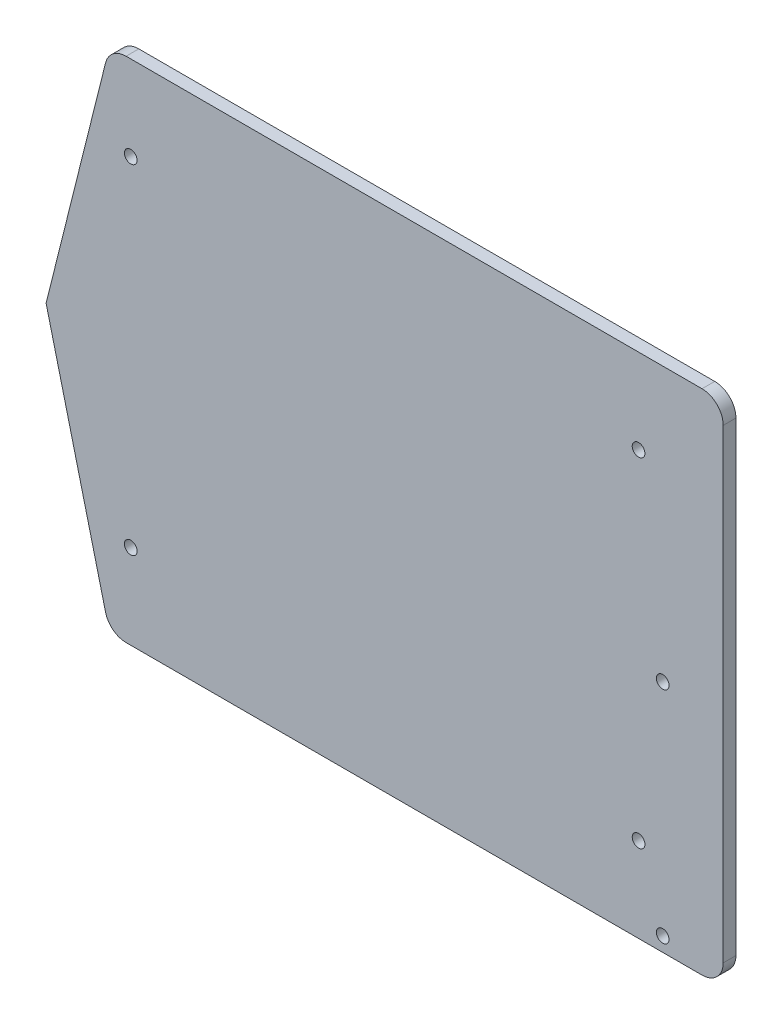
SolidWorks part; units mm, degrees
ref_plane "前基準面" through (0, 0, 0) normal (0, 0, 1) x (1, 0, 0)
ref_plane "上基準面" through (0, 0, 0) normal (0, 1, 0) x (1, 0, 0)
ref_plane "右基準面" through (0, 0, 0) normal (1, 0, 0) x (0, 0, -1)
sketch "草圖1" plane through (0, 0, 0) normal (0, 0, 1) x (1, 0, 0)
  line L1 (15, 120) -> (160, 120)
  line L2 (160, 120) -> (160, 0)
  line L3 (160, 0) -> (15, 0)
  line L4 (0, 60) -> (15, 0)
  line L6 (0, 60) -> (15, 120)
  circle A0 centre (20, 20) radius 1.5
  circle A1 centre (20, 100) radius 1.5
  circle A2 centre (140, 20) radius 1.5
  circle A3 centre (140, 100) radius 1.5
  point P7 (15, 0)
  point P9 (20, 20)
  dimension "D5" = 3
  dimension "D1" = 120
  dimension "D2" = 160
  dimension "D3" = 20
  dimension "D4" = 20
  dimension "D6" = 20
  dimension "D8" = 20
extrude "填料-伸長1" add sketch "草圖1" along normal blind 3
fillet "圓角1" radius 5 4 edges at (15, 0, 1.5) (160, 0, 1.5) (160, 120, 1.5) (15, 120, 1.5)
sketch "草圖2" plane through (0, 0, 3) normal (0, 0, 1) x (1, 0, 0)
  line L0 (160, 5) -> (160, 115) construction
  line L1 (18.9039, 0) -> (155, 0) construction
  circle A0 centre (145.7, 3.38) radius 1.5
  circle A1 centre (145.7, 55.38) radius 1.5
  point P0 (145.7, 3.38)
  point P1 (145.7, 55.38)
  dimension "D1" = 14.3
  dimension "D2" = 3.38
  dimension "D3" = 52
extrude "除料-伸長1" cut sketch "草圖2" against normal blind 10
